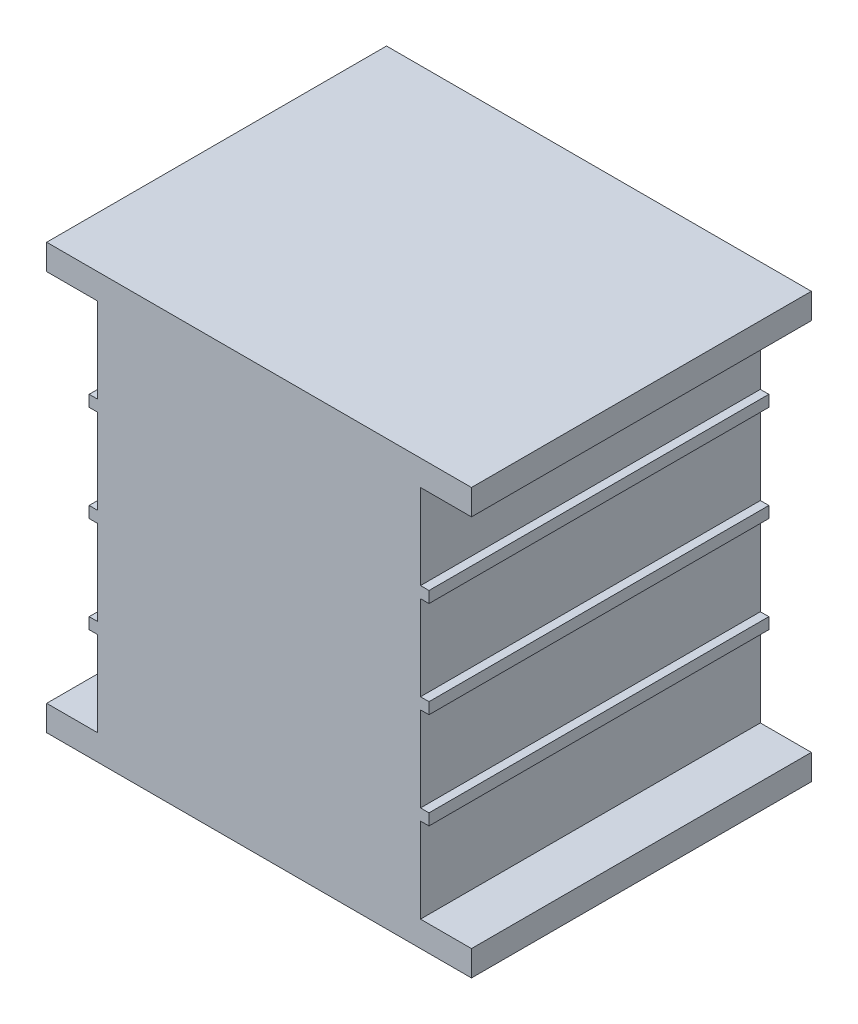
SolidWorks part; units mm, degrees
ref_plane "Front Plane" through (0, 0, 0) normal (0, 0, 1) x (1, 0, 0)
ref_plane "Top Plane" through (0, 0, 0) normal (0, 1, 0) x (1, 0, 0)
ref_plane "Right Plane" through (0, 0, 0) normal (1, 0, 0) x (0, 0, -1)
sketch "Sketch2" plane through (0, 0, 0) normal (0, 0, 1) x (1, 0, 0)
  line L0 (0, 0) -> (25, 0)
  line L1 (25, 0) -> (25, 1.5)
  line L2 (25, 1.5) -> (22, 1.5)
  line L3 (22, 1.5) -> (22, 6.5)
  line L4 (22, 6.5) -> (22.5, 6.5)
  line L5 (22.5, 6.5) -> (22.5, 7.1667)
  line L6 (22.5, 7.1667) -> (22, 7.1667)
  line L7 (22, 7.1667) -> (22, 12.1667)
  line L8 (22, 12.1667) -> (22.5, 12.1667)
  line L9 (22.5, 12.1667) -> (22.5, 12.8333)
  line L10 (22.5, 12.8333) -> (22, 12.8333)
  line L11 (22, 12.8333) -> (22, 17.8333)
  line L12 (22, 17.8333) -> (22.5, 17.8333)
  line L13 (22.5, 17.8333) -> (22.5, 18.5)
  line L14 (22.5, 18.5) -> (22, 18.5)
  line L15 (22, 18.5) -> (22, 23.5)
  line L16 (22, 23.5) -> (25, 23.5)
  line L17 (25, 23.5) -> (25, 25)
  line L18 (25, 25) -> (0, 25)
  line L19 (0, 25) -> (0, 23.5)
  line L20 (0, 23.5) -> (3, 23.5)
  line L21 (3, 23.5) -> (3, 18.5)
  line L22 (3, 18.5) -> (2.5, 18.5)
  line L23 (2.5, 18.5) -> (2.5, 17.8333)
  line L24 (2.5, 17.8333) -> (3, 17.8333)
  line L25 (3, 17.8333) -> (3, 12.8333)
  line L26 (3, 12.8333) -> (2.5, 12.8333)
  line L27 (2.5, 12.8333) -> (2.5, 12.1667)
  line L28 (2.5, 12.1667) -> (3, 12.1667)
  line L29 (3, 12.1667) -> (3, 7.1667)
  line L30 (3, 7.1667) -> (2.5, 7.1667)
  line L31 (2.5, 7.1667) -> (2.5, 6.5)
  line L32 (2.5, 6.5) -> (3, 6.5)
  line L33 (3, 6.5) -> (3, 1.5)
  line L34 (3, 1.5) -> (0, 1.5)
  line L35 (0, 1.5) -> (0, 0)
  line L36 (3, 18.5) -> (22, 18.5) construction
  line L37 (3, 17.8333) -> (22, 17.8333) construction
  line L39 (3, 12.8333) -> (22, 12.8333) construction
  line L40 (3, 12.1667) -> (22, 12.1667) construction
  line L41 (3, 7.1667) -> (22, 7.1667) construction
  line L42 (22, 6.5) -> (3, 6.5) construction
  dimension "D1" = 5
  dimension "D2" = 25
  dimension "D3" = 0.5
  dimension "D4" = 25
  dimension "D5" = 3
  dimension "D6" = 1.5
extrude "Boss-Extrude1" add sketch "Sketch2" along normal blind 20
